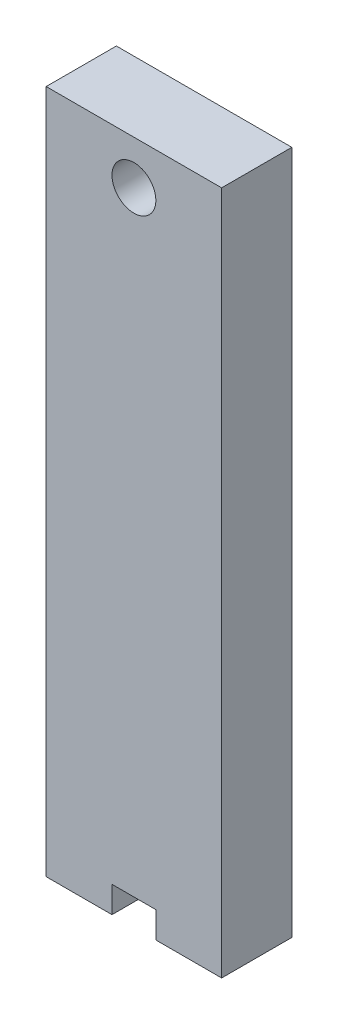
SolidWorks part; units mm, degrees
ref_plane "Front Plane" through (0, 0, 0) normal (0, 0, 1) x (1, 0, 0)
ref_plane "Top Plane" through (0, 0, 0) normal (0, 1, 0) x (1, 0, 0)
ref_plane "Right Plane" through (0, 0, 0) normal (1, 0, 0) x (0, 0, -1)
sketch "Sketch2" plane through (0, 0, 0) normal (0, 1, 0) x (1, 0, 0)
  line L0 (-8, 2) -> (-8, -2)
  line L1 (-10, 4) -> (10, 4)
  line L2 (-10, 4) -> (-10, -4)
  line L3 (-10, -4) -> (10, -4)
  line L4 (10, 4) -> (10, -4)
  line L5 (-10, 4) -> (10, -4) construction
  line L6 (-10, -4) -> (10, 4) construction
  line L7 (-8, -2) -> (8, -2)
  line L8 (8, 2) -> (8, -2)
  line L9 (-8, 2) -> (8, 2)
  point P0 (0, 0)
  dimension "D1" = 20
  dimension "D2" = 8
  dimension "D3" = 2
extrude "Boss-Extrude2" add sketch "Sketch2" along normal blind 65
sketch "Sketch4" plane through (0, 0, -4) normal (0, 0, -1) x (-1, 0, 0)
  line L0 (0, 65) -> (0, 0) construction
  line L1 (-10, 65) -> (10, 65) construction
  line L2 (-10, 0) -> (10, 0) construction
  line L3 (8, 60) -> (-8, 60)
  line L4 (-8, 60) -> (-8, 57.5)
  line L5 (-8, 57.5) -> (-2.5, 57.5)
  line L6 (-2.5, 57.5) -> (-2.5, 0)
  line L7 (-2.5, 0) -> (2.5, 0)
  line L8 (2.5, 57.5) -> (2.5, 0)
  line L9 (8, 60) -> (8, 57.5)
  line L10 (8, 57.5) -> (2.5, 57.5)
  point P13 (0, 0)
  point P16 (0, 60)
  dimension "D1" = 8
  dimension "D2" = 2.5
  dimension "D3" = 0
  dimension "D4" = 2.5
  dimension "D5" = 5
extrude "Cut-Extrude2" cut sketch "Sketch4" against normal up to surface (2 mm away) up to face at (0, 32.5, -2)
sketch "Sketch5" plane through (0, 0, 0) normal (0, -1, 0) x (1, 0, 0)
  line L0 (10, 4) -> (10, -4) construction
  line L1 (-10, 4) -> (-2.5, 4)
  line L2 (-10, 4) -> (-10, -4)
  line L3 (-10, -4) -> (-2.5, -4)
  line L4 (-2.5, 4) -> (-2.5, -4)
  line L5 (2.5, -4) -> (10, -4)
  line L6 (2.5, -4) -> (2.5, 4)
  line L7 (2.5, 4) -> (10, 4)
  line L8 (10, -4) -> (10, 4)
  line L9 (-10, 4) -> (10, 4) construction
extrude "Boss-Extrude3" add sketch "Sketch5" along normal blind 3
sketch "Sketch6" plane through (0, 65, 0) normal (0, 1, 0) x (1, 0, 0)
  line L1 (-10, 4) -> (10, 4)
  line L2 (-10, 4) -> (-10, -4)
  line L3 (-10, -4) -> (10, -4)
  line L4 (10, 4) -> (10, -4)
extrude "Boss-Extrude4" add sketch "Sketch6" along normal blind 10
sketch "Sketch7" plane through (0, 0, -4) normal (0, 0, -1) x (-1, 0, 0)
  line L0 (-10, 75) -> (10, 75) construction
  circle A0 centre (0, 70) radius 2.5
  dimension "D1" = 5
  dimension "D2" = 5
extrude "Cut-Extrude3" cut sketch "Sketch7" against normal through all both and the other way through all
